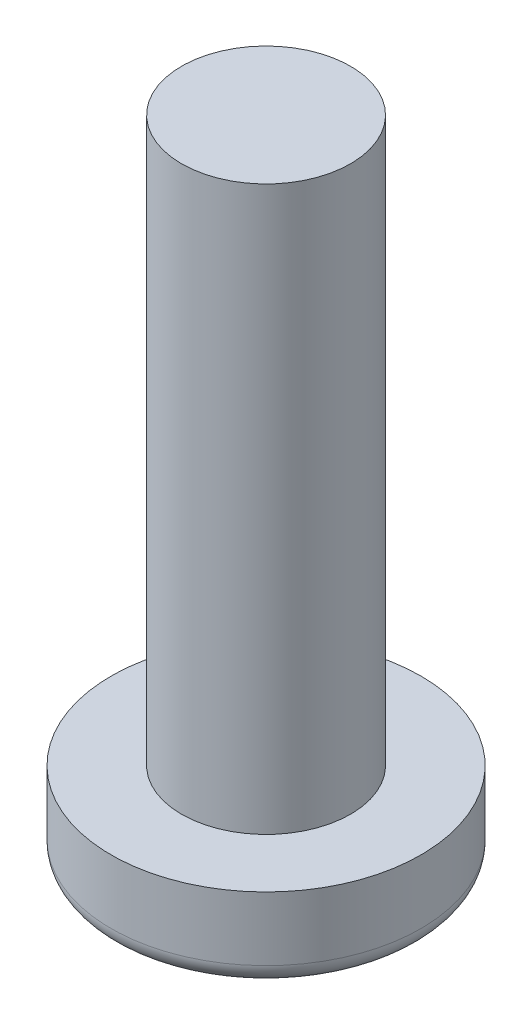
SolidWorks part; units mm, degrees
ref_plane "前视基准面" through (0, 0, 0) normal (0, 0, 1) x (1, 0, 0)
ref_plane "上视基准面" through (0, 0, 0) normal (0, 1, 0) x (1, 0, 0)
ref_plane "右视基准面" through (0, 0, 0) normal (1, 0, 0) x (0, 0, -1)
sketch "草图1" plane through (0, 0, 0) normal (0, 0, 1) x (1, 0, 0)
  line L0 (2.75, 1.5) -> (0, 1.5)
  line L1 (0, 1.5) -> (0, 0)
  line L2 (0, 0) -> (2.75, 0)
  line L3 (2.75, 0) -> (2.75, 1.5)
  line L4 (0, 1.5) -> (0, 0) construction
revolve "旋转1" add sketch "草图1" angle 360 about L4
sketch "草图2" plane through (0, 1.5, 0) normal (0, 1, 0) x (-1, 0, 0)
  circle A0 centre (0, 0) radius 1.5
extrude "凸台-拉伸1" add sketch "草图2" along normal blind 10
fillet "圆角1" radius 0.3673 1 edges at (0, 0, -2.75)
